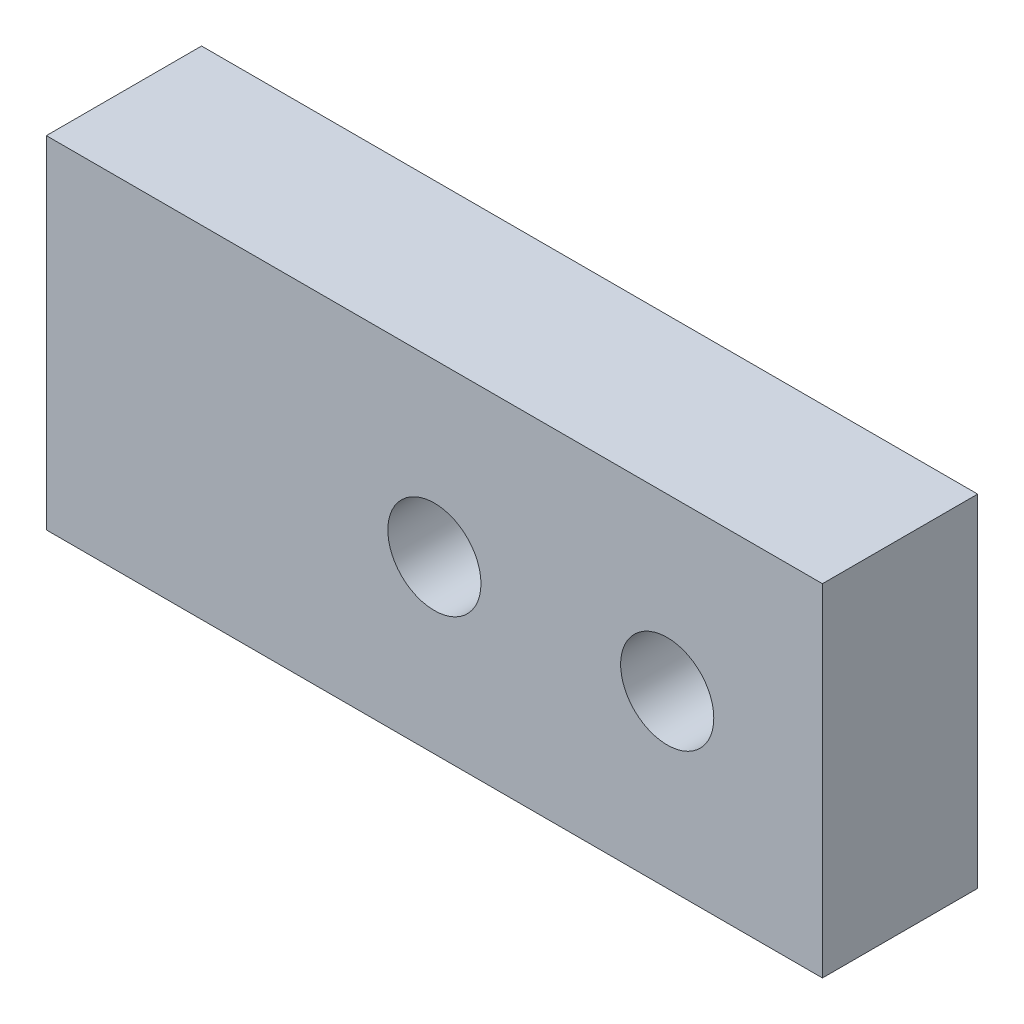
SolidWorks part; units mm, degrees
ref_plane "Front Plane" through (0, 0, 0) normal (0, 0, 1) x (1, 0, 0)
ref_plane "Top Plane" through (0, 0, 0) normal (0, 1, 0) x (1, 0, 0)
ref_plane "Right Plane" through (0, 0, 0) normal (1, 0, 0) x (0, 0, -1)
sketch "Sketch1" plane through (0, 0, 0) normal (0, 0, 1) x (1, 0, 0)
  line L1 (-25, -11) -> (25, -11)
  line L2 (-25, -11) -> (-25, 11)
  line L3 (-25, 11) -> (25, 11)
  line L4 (25, -11) -> (25, 11)
  line L5 (-25, -11) -> (25, 11) construction
  line L6 (-25, 11) -> (25, -11) construction
  point P0 (0, 0)
  dimension "D1" = 50
  dimension "D2" = 22
extrude "Boss-Extrude1" add sketch "Sketch1" along normal blind 10
hole_wizard "M5 Tapped Hole1" positions "Sketch3" profile "Sketch4" tap size "M5" standard "ISO"
sketch "Sketch3" plane through (-25, 0, 0) normal (-1, 0, 0) x (0, 0, 1)
  line L0 (10, -11) -> (0, -11) construction
  line L1 (0, 11) -> (0, -11) construction
  line L2 (10, 11) -> (0, 11) construction
  point P0 (5, -6)
  point P2 (5, 6)
  dimension "D1" = 5
  dimension "D2" = 5
  dimension "D3" = 5
  dimension "D4" = 5
sketch "Sketch4" plane through (-25, -6, 5) normal (0, 1, 0) x (0, 0, 1)
  line L0 (0, 0) -> (0, 15.2618)
  line L1 (0, 15.2618) -> (2.1, 14)
  line L2 (2.1, 14) -> (2.1, 0)
  line L5 (2.1, 0) -> (0, 0)
  line L10 (0, 15.2618) -> (-2.1, 14) construction
  line L11 (0, -6.35) -> (0, 107.95) construction
  dimension "Tap Drill Dia." = 4.2
  dimension "Tap Drill Depth" = 14
  dimension "Drill Angle" = 118
cosmetic thread "Hole Thread1" parameters "D1"=10, "D2"=5
cosmetic thread "Hole Thread2" parameters "D1"=10, "D2"=5
sketch "Sketch5" plane through (0, 0, 10) normal (0, 0, 1) x (1, 0, 0)
  line L0 (25, -11) -> (25, 11) construction
  circle A0 centre (15, 0) radius 3
  circle A1 centre (0, 0) radius 3
  dimension "D1" = 6
  dimension "D2" = 6
  dimension "D3" = 10
  dimension "D4" = 15
extrude "Cut-Extrude1" cut sketch "Sketch5" against normal blind 10
